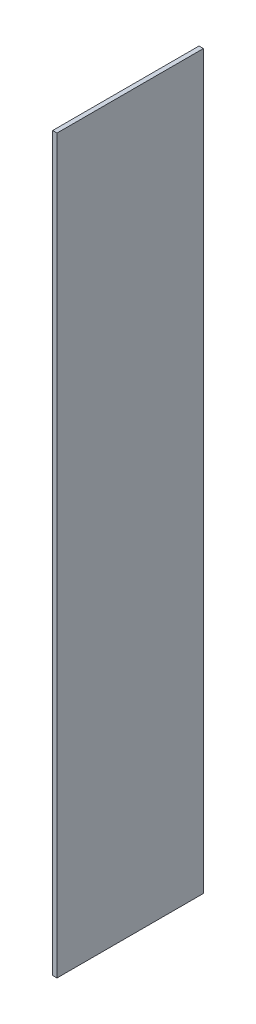
SolidWorks part; units mm, degrees
ref_plane "Front Plane" through (0, 0, 0) normal (0, 0, 1) x (1, 0, 0)
ref_plane "Top Plane" through (0, 0, 0) normal (0, 1, 0) x (1, 0, 0)
ref_plane "Right Plane" through (0, 0, 0) normal (1, 0, 0) x (0, 0, -1)
sketch "Sketch1" plane through (0, 0, 0) normal (0, 1, 0) x (1, 0, 0)
  line L1 (-0.75, 25) -> (0.75, 25)
  line L2 (-0.75, 25) -> (-0.75, -25)
  line L3 (-0.75, -25) -> (0.75, -25)
  line L4 (0.75, 25) -> (0.75, -25)
  line L5 (-0.75, 25) -> (0.75, -25) construction
  line L6 (-0.75, -25) -> (0.75, 25) construction
  point P0 (0, 0)
  dimension "D1" = 50
  dimension "D2" = 1.5
extrude "Boss-Extrude1" add sketch "Sketch1" along normal mid plane 250
